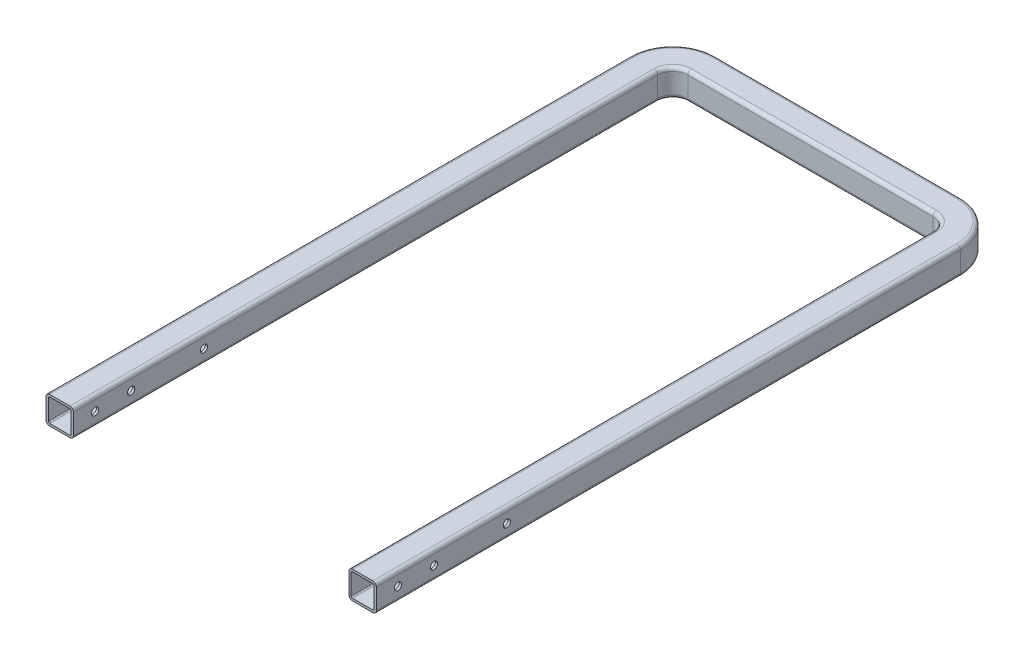
SolidWorks part; units mm, degrees
material "5052-H38, Rod (SS)"
ref_plane "Front Plane" through (0, 0, 0) normal (0, 0, 1) x (1, 0, 0)
ref_plane "Top Plane" through (0, 0, 0) normal (0, 1, 0) x (1, 0, 0)
ref_plane "Right Plane" through (0, 0, 0) normal (1, 0, 0) x (0, 0, -1)
sketch "Sketch1" plane through (0, 0, 0) normal (0, 1, 0) x (1, 0, 0)
  line L0 (0, 0) -> (0, 810)
  line L1 (40, 850) -> (380, 850)
  line L2 (420, 810) -> (420, 0)
  line L3 (0, 560) -> (420, 560) construction
  line L4 (0, 260) -> (420, 260) construction
  line L5 (420, 260) -> (420, 560) construction
  arc A0 (380, 850) -> (420, 810) centre (380, 810) cw
  arc A1 (40, 850) -> (0, 810) centre (40, 810) ccw
  point P7 (420, 850)
  point P10 (0, 850)
  dimension "D3" = 40
  dimension "D4" = 250
  dimension "D1" = 850
  dimension "D2" = 420
  dimension "D5" = 300
ref_plane "Plane1" through (0, 0, 0) normal (0, 0, 1) x (1, 0, 0)
sketch "Sketch3" plane through (0, 0, 0) normal (0, 0, 1) x (1, 0, 0)
  line L1 (-14.05, -19.05) -> (14.05, -19.05)
  line L2 (-19.05, -14.05) -> (-19.05, 14.05)
  line L3 (-14.05, 19.05) -> (14.05, 19.05)
  line L4 (19.05, -14.05) -> (19.05, 14.05)
  line L5 (-19.05, -19.05) -> (19.05, 19.05) construction
  line L6 (-19.05, 19.05) -> (19.05, -19.05) construction
  arc A0 (-14.05, 19.05) -> (-19.05, 14.05) centre (-14.05, 14.05) ccw
  arc A1 (-19.05, -14.05) -> (-14.05, -19.05) centre (-14.05, -14.05) ccw
  arc A2 (14.05, -19.05) -> (19.05, -14.05) centre (14.05, -14.05) ccw
  arc A3 (19.05, 14.05) -> (14.05, 19.05) centre (14.05, 14.05) ccw
  point P0 (0, 0)
  dimension "D3" = 5
  dimension "D1" = 38.1
  dimension "D2" = 38.1
sweep "Sweep-Thin1" add profiles "Sketch3" path "Sketch1" parameters "D1"=3.175
sketch "Sketch4" plane through (0, 0, 0) normal (1, 0, 0) x (0, 0, -1)
  line L0 (0, 0) -> (810, 0) construction
  circle A0 centre (30, 0) radius 5
  circle A1 centre (80, 0) radius 5
  circle A2 centre (180.9551, 0) radius 5
  dimension "D1" = 30
  dimension "D3" = 10
  dimension "D2" = 80
extrude "Cut-Extrude2" cut sketch "Sketch4" against normal through all both and the other way through all
ref_plane "Plane4" through (420, 0, 0) normal (-1, 0, 0) x (0, 0, 1)
sketch "Sketch8" plane through (420, 0, 0) normal (-1, 0, 0) x (0, 0, 1)
  line L0 (-560, 0) -> (-260, 0) construction
  line L1 (-410, 0) -> (-410, -61.9086) construction
ref_plane "Plane5" through (0, 0, 0) normal (1, 0, 0) x (0, 0, -1)
